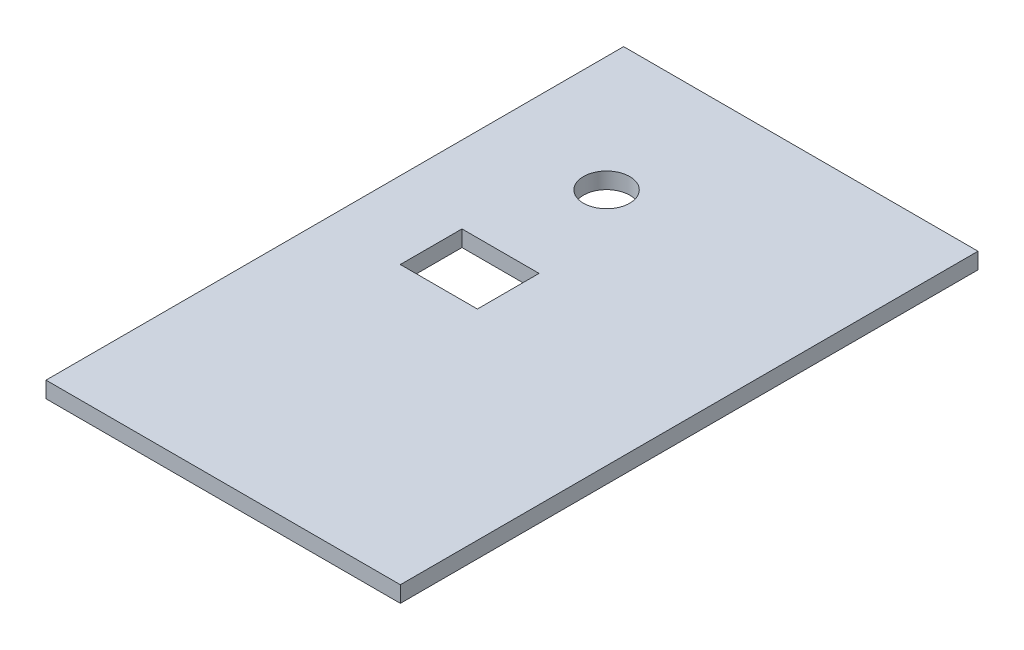
SolidWorks part; units mm, degrees
ref_plane "Front Plane" through (0, 0, 0) normal (0, 0, 1) x (1, 0, 0)
ref_plane "Top Plane" through (0, 0, 0) normal (0, 1, 0) x (1, 0, 0)
ref_plane "Right Plane" through (0, 0, 0) normal (1, 0, 0) x (0, 0, -1)
sketch "Sketch1" plane through (0, 0, 0) normal (0, 1, 0) x (1, 0, 0)
  line L0 (-11.5025, 18.75) -> (11.5025, -18.75) construction
  line L1 (-11.5025, 18.75) -> (11.5025, 18.75)
  line L2 (-11.5025, 18.75) -> (-11.5025, -18.75)
  line L3 (-11.5025, -18.75) -> (11.5025, -18.75)
  line L4 (11.5025, 18.75) -> (11.5025, -18.75)
  line L5 (-6.5025, 1.2525) -> (-1.4975, 1.2525) construction
  line L6 (-6.5025, 3.255) -> (-1.4975, 3.255)
  line L7 (-6.5025, 3.255) -> (-6.5025, -0.75)
  line L8 (-6.5025, -0.75) -> (-1.4975, -0.75)
  line L9 (-1.4975, 3.255) -> (-1.4975, -0.75)
  circle A0 centre (-4.0025, 10.1427) radius 1.5025
  dimension "D6" = 3.005
  dimension "D7" = 8.8902
  dimension "D1" = 5.005
  dimension "D2" = 4.005
  dimension "D3" = 23.005
  dimension "D4" = 37.5
  dimension "D5" = 18
  dimension "D8" = 5
  dimension "D9" = 7.5
extrude "Boss-Extrude1" add sketch "Sketch1" along normal blind 1.05
